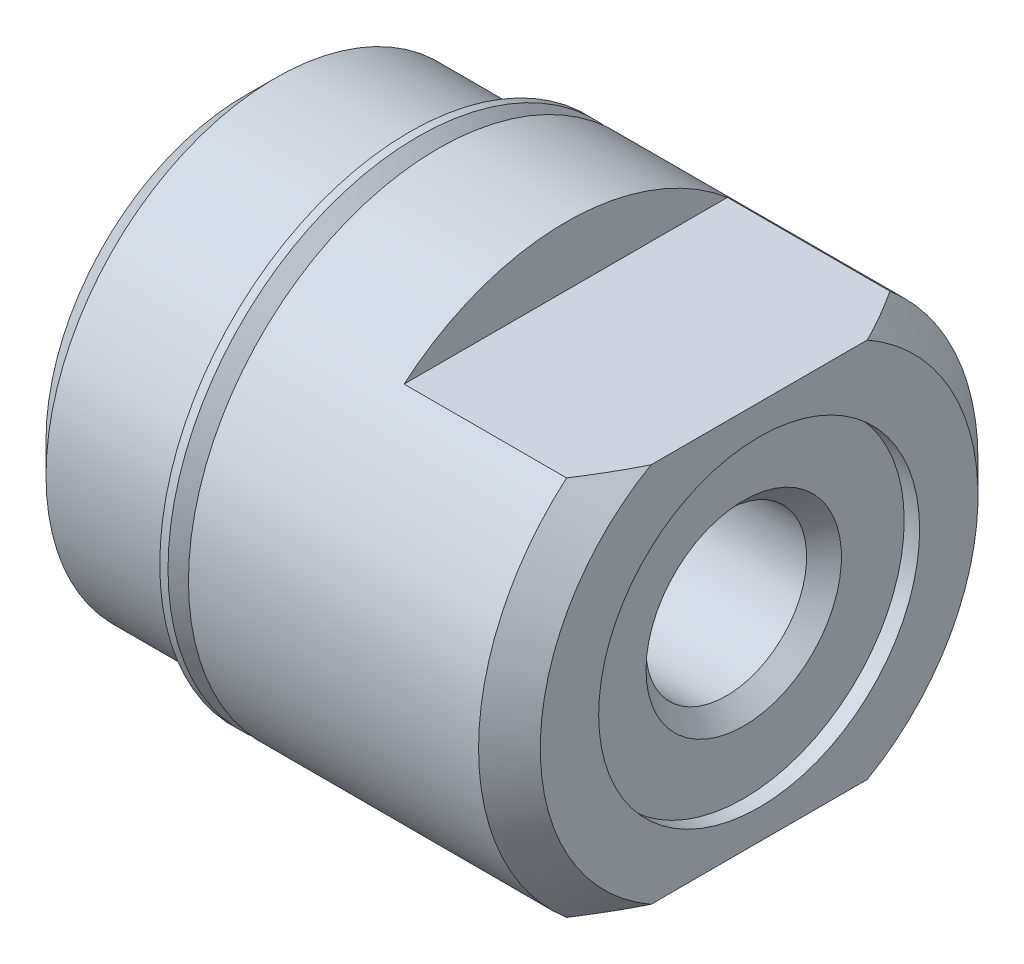
SolidWorks part; units mm, degrees
ref_plane "Front Plane" through (0, 0, 0) normal (0, 0, 1) x (1, 0, 0)
ref_plane "Top Plane" through (0, 0, 0) normal (0, 1, 0) x (1, 0, 0)
ref_plane "Right Plane" through (0, 0, 0) normal (1, 0, 0) x (0, 0, -1)
ref_plane "Plane1" through (0, 0, 0) normal (0, 0, 1) x (1, 0, 0)
sketch "Sketch1" plane through (0, 0, 0) normal (0, 0, 1) x (1, 0, 0)
  line L0 (0, 0) -> (0, 4.9085)
  line L1 (0, 4.9085) -> (0.762, 5.6705)
  line L2 (0.762, 5.6705) -> (3.7592, 5.6705)
  line L3 (3.7592, 5.6705) -> (4.2672, 5.1626)
  line L4 (4.2672, 5.1626) -> (4.7752, 5.1626)
  line L5 (4.7752, 5.1626) -> (4.7752, 6.1658)
  line L6 (4.7752, 6.1658) -> (11.938, 6.1658)
  line L7 (11.938, 6.1658) -> (12.7, 5.4039)
  line L8 (12.7, 5.4039) -> (12.7, 0)
  line L9 (12.7, 0) -> (0, 0)
  line L10 (12.7, 0) -> (0, 0) construction
revolve "Revolve1" add sketch "Sketch1" angle 360 about L10
ref_plane "Plane2" through (0, 0, 0) normal (0, 0, 1) x (1, 0, 0)
sketch "Sketch2" plane through (0, 0, 0) normal (0, 0, 1) x (1, 0, 0)
  line L0 (12.319, 0) -> (12.319, 3.9624)
  line L1 (12.319, 3.9624) -> (12.7, 3.9624)
  line L2 (12.7, 3.9624) -> (12.7, 0)
  line L3 (12.7, 0) -> (12.319, 0)
  line L4 (12.7, 0) -> (12.319, 0) construction
revolve "Cut-Revolve1" cut sketch "Sketch2" angle 360 about L4
ref_plane "Plane3" through (0, 0, 0) normal (0, 0, 1) x (1, 0, 0)
sketch "Sketch3" plane through (0, 0, 0) normal (0, 0, 1) x (1, 0, 0)
  line L0 (0, 0) -> (0, 1.9837)
  line L1 (0, 1.9837) -> (11.8897, 1.9837)
  line L2 (11.8897, 1.9837) -> (12.319, 2.413)
  line L3 (12.319, 2.413) -> (12.319, 0)
  line L4 (12.319, 0) -> (0, 0)
  line L5 (12.319, 0) -> (0, 0) construction
revolve "Cut-Revolve2" cut sketch "Sketch3" angle 360 about L5
ref_plane "Plane4" through (12.7, 0, 0) normal (1, 0, 0) x (0, 0, -1)
sketch "Sketch4" plane through (12.7, 0, 0) normal (1, 0, 0) x (0, 0, -1)
  line L0 (-24.6634, -12.3317) -> (24.6634, -12.3317)
  line L1 (24.6634, -12.3317) -> (24.6634, 12.3317)
  line L2 (24.6634, 12.3317) -> (-24.6634, 12.3317)
  line L3 (-24.6634, 12.3317) -> (-24.6634, -12.3317)
  line L4 (-12.3317, -4.699) -> (12.3317, -4.699)
  line L5 (12.3317, -4.699) -> (12.3317, 4.699)
  line L6 (12.3317, 4.699) -> (-12.3317, 4.699)
  line L7 (-12.3317, 4.699) -> (-12.3317, -4.699)
extrude "Cut-Extrude1" cut sketch "Sketch4" against normal blind 4.7752
ref_plane "Plane5" through (0, 0, 0) normal (0, 0, 1) x (1, 0, 0)
sketch "Sketch5" plane through (0, 0, 0) normal (0, 0, 1) x (1, 0, 0)
  line L0 (4.0665, 6.1658) -> (4.0665, 6.0817)
  line L1 (4.0665, 6.0817) -> (4.6636, 5.4846)
  line L2 (4.6636, 5.305) -> (4.5212, 5.1626)
  line L3 (4.5212, 5.1626) -> (4.2672, 5.1626)
  line L4 (4.2672, 5.1626) -> (4.2672, 4.9085)
  line L5 (4.2672, 4.9085) -> (4.7752, 4.9085)
  line L6 (4.7752, 4.9085) -> (4.7752, 5.6603)
  line L7 (4.7752, 5.6603) -> (4.2697, 6.1658)
  line L8 (4.2697, 6.1658) -> (4.0665, 6.1658)
  line L9 (4.7752, 0) -> (4.2672, 0) construction
  arc A0 (4.6636, 5.4846) -> (4.6636, 5.305) centre (4.5738, 5.3948) cw
revolve "Revolve2" add sketch "Sketch5" angle 360 about L9
